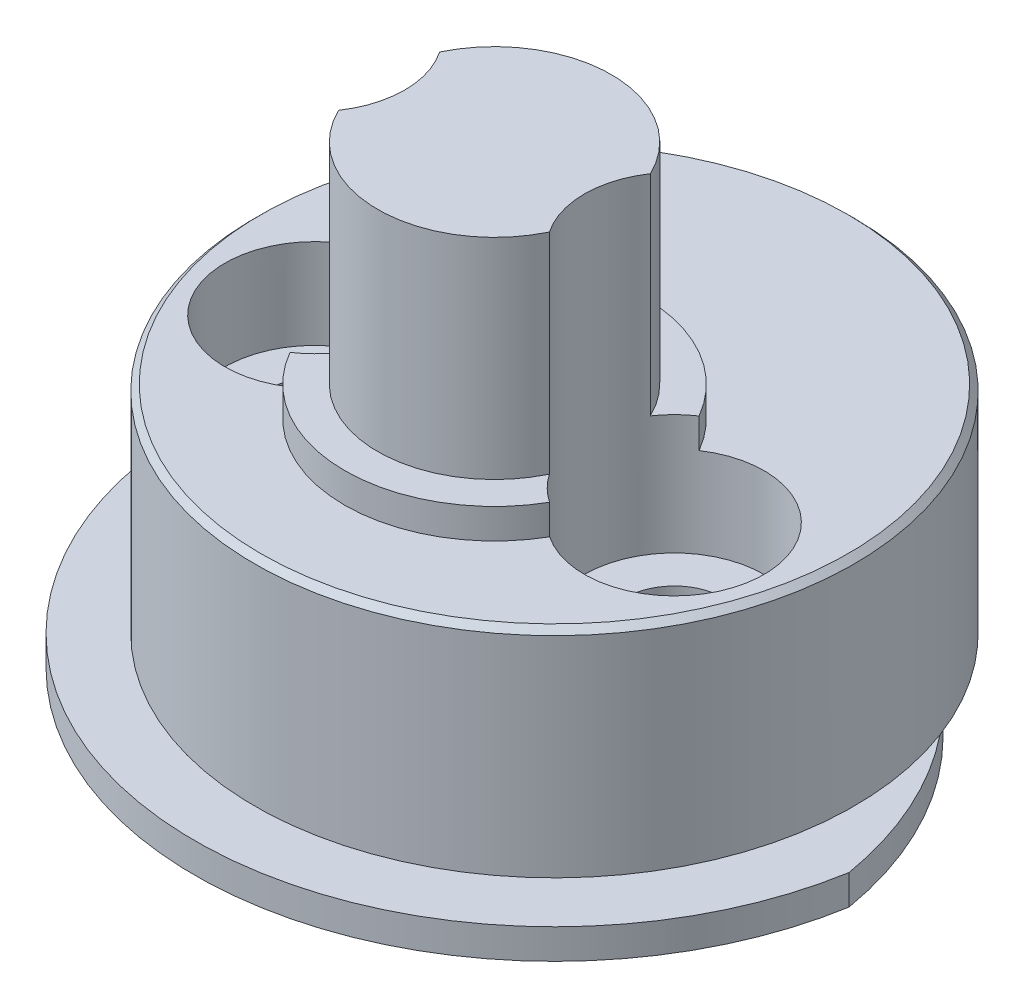
SolidWorks part; units mm, degrees
ref_plane "Front Plane" through (0, 0, 0) normal (0, 0, 1) x (1, 0, 0)
ref_plane "Top Plane" through (0, 0, 0) normal (0, 1, 0) x (1, 0, 0)
ref_plane "Right Plane" through (0, 0, 0) normal (1, 0, 0) x (0, 0, -1)
sketch "Sketch1" plane through (0, 0, 0) normal (0, 1, 0) x (1, 0, 0)
  line L1 (-2.75, -5.25) -> (2.75, -5.25)
  line L2 (-2.75, -5.25) -> (-2.75, 5.25)
  line L3 (-2.75, 5.25) -> (2.75, 5.25)
  line L4 (2.75, -5.25) -> (2.75, 5.25)
  line L5 (-2.75, -5.25) -> (2.75, 5.25) construction
  line L6 (-2.75, 5.25) -> (2.75, -5.25) construction
  circle A0 centre (-6, 0) radius 1.65
  circle A1 centre (6, 0) radius 1.65
  arc A2 (-11.8322, 0) -> (11.8322, 0) centre (0, 2) ccw
  arc A3 (11.8322, 0) -> (-11.8322, 0) centre (0, -2) ccw
  point P0 (0, 0)
  dimension "D5" = 3.3
  dimension "D6" = 24
  dimension "D8" = 24
  dimension "D1" = 5.5
  dimension "D2" = 10.5
  dimension "D3" = 6
  dimension "D4" = 6
  dimension "D7" = 2
  dimension "D9" = 2
extrude "Boss-Extrude1" add sketch "Sketch1" along normal blind 1
sketch "Sketch2" plane through (0, 1, 0) normal (0, 1, 0) x (1, 0, 0)
  line L4 (2.75, 5.25) -> (-2.75, 5.25)
  line L5 (2.75, -5.25) -> (2.75, 5.25)
  line L6 (-2.75, -5.25) -> (2.75, -5.25)
  line L7 (-2.75, 5.25) -> (-2.75, -5.25)
  line L8 (2.75, 5.25) -> (-2.75, 5.25)
  line L9 (2.75, -5.25) -> (2.75, 5.25)
  line L10 (-2.75, -5.25) -> (2.75, -5.25)
  line L11 (-2.75, 5.25) -> (-2.75, -5.25)
  circle A0 centre (0, 2) radius 10
  circle A2 centre (6, 0) radius 1.65
  circle A3 centre (6, 0) radius 1.65
  circle A4 centre (-6, 0) radius 1.65
  circle A5 centre (-6, 0) radius 1.65
  dimension "D1" = 20
  dimension "D2" = 2
  dimension "D3" = 0
  dimension "D4" = 0
  dimension "D5" = 0
extrude "Boss-Extrude2" add sketch "Sketch2" along normal blind 4.2
sketch "Sketch3" plane through (0, 5.2, 0) normal (0, 1, 0) x (1, 0, 0)
  circle A0 centre (0, 2) radius 10 construction
  circle A1 centre (6, 0) radius 1.65
  circle A2 centre (6, 0) radius 1.65
  circle A3 centre (-6, 0) radius 1.65
  circle A4 centre (-6, 0) radius 1.65
  circle A5 centre (0, 2) radius 10
  dimension "D1" = 0
  dimension "D2" = 0
extrude "Boss-Extrude3" add sketch "Sketch3" along normal blind 3
sketch "Sketch4" plane through (0, 8.2, 0) normal (0, 1, 0) x (1, 0, 0)
  circle A0 centre (0, 0) radius 5
  dimension "D1" = 10
extrude "Boss-Extrude4" add sketch "Sketch4" along normal blind 1
sketch "Sketch5" plane through (0, 9.2, 0) normal (0, 1, 0) x (1, 0, 0)
  circle A0 centre (0, 0) radius 3.9
  dimension "D1" = 7.8
extrude "Boss-Extrude5" add sketch "Sketch5" along normal blind 7
sketch "Sketch6" plane through (0, 9.2, 0) normal (0, 1, 0) x (1, 0, 0)
  circle A0 centre (-6, 0) radius 3
  circle A1 centre (6, 0) radius 3
  dimension "D1" = 6
extrude "Cut-Extrude1" cut sketch "Sketch6" against normal blind 4 and the other way blind 10
chamfer "Chamfer1" distance 0.2 angle 45 1 edges at (0, 8.2, 8)
